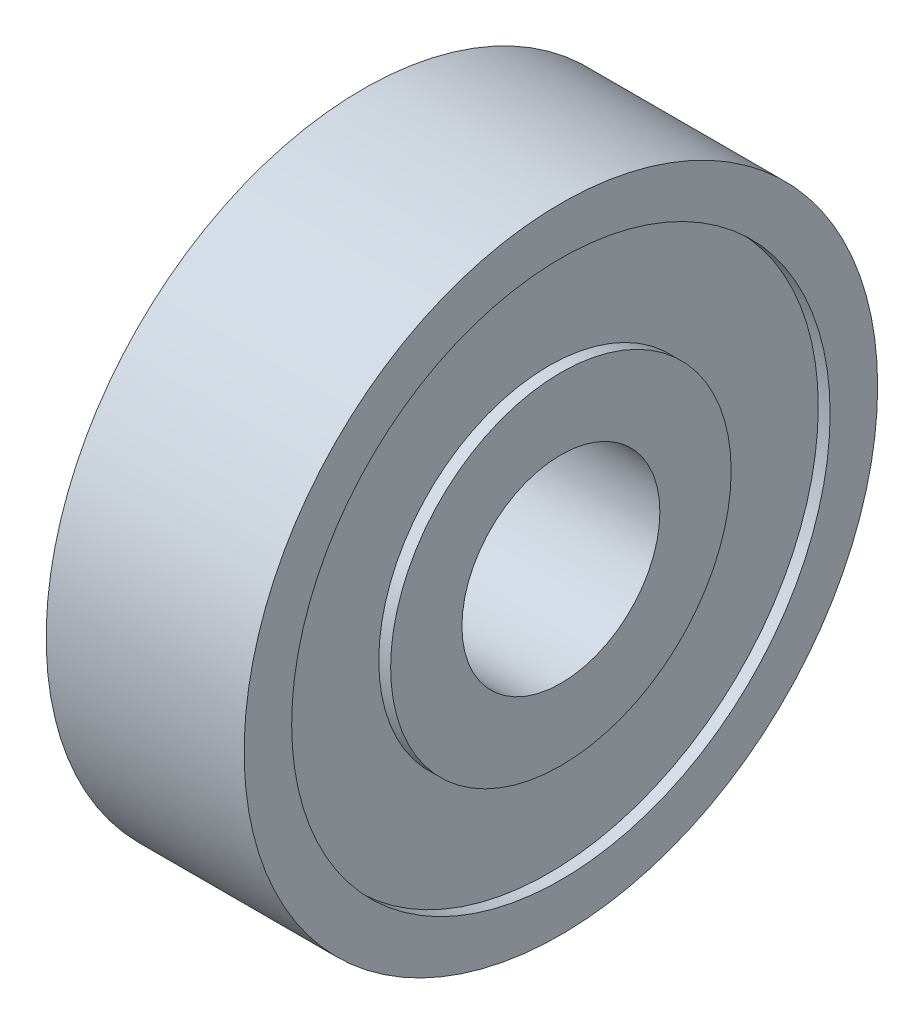
SolidWorks part; units mm, degrees
material "Plain Carbon Steel"
ref_plane "Front Plane" through (0, 0, 0) normal (0, 0, 1) x (1, 0, 0)
ref_plane "Top Plane" through (0, 0, 0) normal (0, 1, 0) x (1, 0, 0)
ref_plane "Right Plane" through (0, 0, 0) normal (1, 0, 0) x (0, 0, -1)
sketch "Sketch1" plane through (0, 0, 0) normal (0, 0, 1) x (1, 0, 0)
  line L0 (2.5, 2.5) -> (-2.5, 2.5)
  line L1 (-2.5, 2.5) -> (-2.5, 4.3)
  line L2 (-2.5, 4.3) -> (-2.2, 4.3)
  line L3 (-2.2, 4.3) -> (-2.2, 6.8)
  line L4 (-2.2, 6.8) -> (-2.5, 6.8)
  line L5 (-2.5, 6.8) -> (-2.5, 8)
  line L6 (-2.5, 8) -> (2.5, 8)
  line L7 (0, 8) -> (0, 2.5) construction
  line L8 (2.5, 6.8) -> (2.5, 8)
  line L9 (2.2, 6.8) -> (2.5, 6.8)
  line L10 (2.2, 4.3) -> (2.2, 6.8)
  line L11 (2.5, 4.3) -> (2.2, 4.3)
  line L12 (2.5, 2.5) -> (2.5, 4.3)
  line L13 (0, 0) -> (-4.3663, 0) construction
  dimension "D1" = 5
  dimension "D2" = 16
  dimension "D3" = 5
  dimension "D4" = 8.6
  dimension "D5" = 2.5
  dimension "D6" = 0.3
revolve "Revolve1" add sketch "Sketch1" angle 360 about L13
